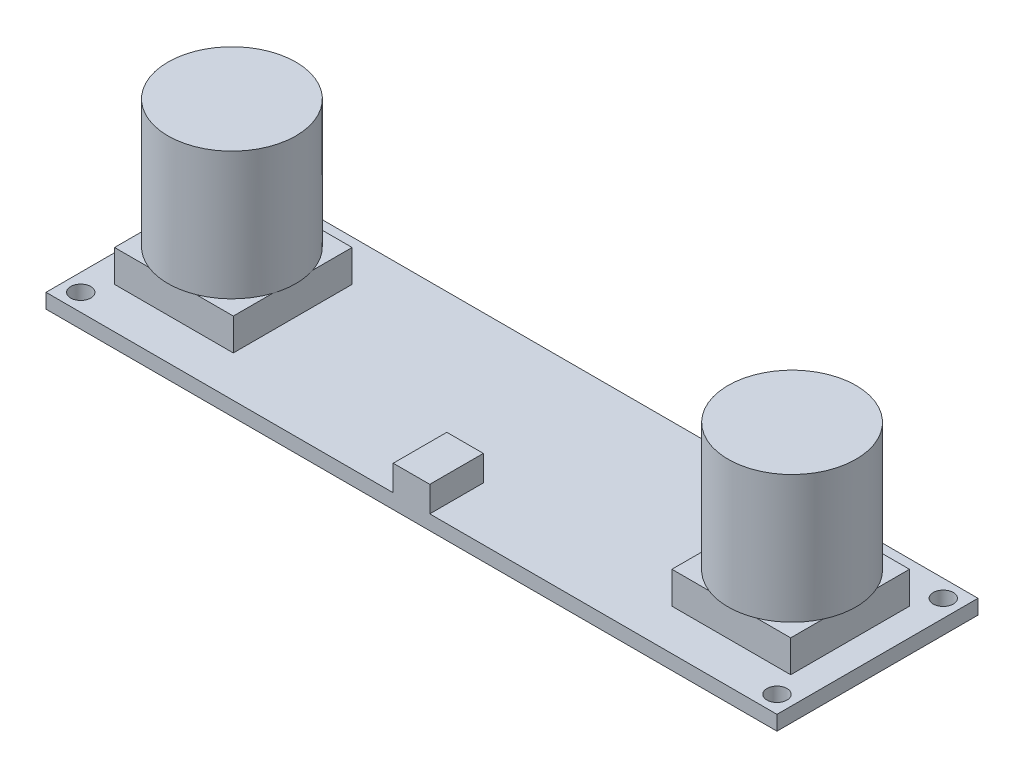
SolidWorks part; units mm, degrees
ref_plane "前视基准面" through (0, 0, 0) normal (0, 0, 1) x (1, 0, 0)
ref_plane "上视基准面" through (0, 0, 0) normal (0, 1, 0) x (1, 0, 0)
ref_plane "右视基准面" through (0, 0, 0) normal (1, 0, 0) x (0, 0, -1)
other "Configuration Table"
sketch "草图1" plane through (0, 0, 0) normal (0, 1, 0) x (1, 0, 0)
  line L1 (40, -11) -> (-40, -11)
  line L2 (40, -11) -> (40, 11)
  line L3 (40, 11) -> (-40, 11)
  line L4 (-40, -11) -> (-40, 11)
  line L5 (40, -11) -> (-40, 11) construction
  line L6 (40, 11) -> (-40, -11) construction
  point P0 (0, 0)
  dimension "D1" = 80
  dimension "D2" = 22
extrude "凸台-拉伸1" add sketch "草图1" along normal blind 1.6
sketch "草图2" plane through (0, 1.6, 0) normal (0, 1, 0) x (1, 0, 0)
  line L0 (-40, 0) -> (40, 0) construction
  line L1 (-40, 11) -> (-40, -11) construction
  line L2 (40, -11) -> (40, 11) construction
  line L3 (0, 11) -> (0, -11) construction
  line L4 (40, 11) -> (-40, 11) construction
  line L5 (-40, -11) -> (40, -11) construction
  line L6 (37, -6.5) -> (37, 6.5)
  line L7 (-24, -6.5) -> (-37, -6.5)
  line L8 (-24, -6.5) -> (-24, 6.5)
  line L9 (-24, 6.5) -> (-37, 6.5)
  line L10 (-37, -6.5) -> (-37, 6.5)
  line L11 (-24, -6.5) -> (-37, 6.5) construction
  line L12 (-24, 6.5) -> (-37, -6.5) construction
  line L13 (24, -6.5) -> (37, -6.5)
  line L14 (24, -6.5) -> (24, 6.5)
  line L15 (24, 6.5) -> (37, 6.5)
  point P12 (-30.5, 0)
  dimension "D1" = 3
  dimension "D2" = 13
extrude "凸台-拉伸2" add sketch "草图2" along normal blind 3.5
ref_plane "基准面1" through (0, 5.1, 0) normal (0, 1, 0) x (1, 0, 0)
sketch "草图4" plane through (0, 5.1, 0) normal (0, 1, 0) x (1, 0, 0)
  line L0 (-38.1, 0) -> (-23.2, 0) construction
  line L5 (0, 11) -> (0, -11) construction
  line L6 (40, 11) -> (-40, 11) construction
  line L7 (-40, -11) -> (40, -11) construction
  circle A0 centre (-30.65, 0) radius 7
  circle A1 centre (30.65, 0) radius 7
extrude "凸台-拉伸3" add sketch "草图4" along normal blind 14
sketch "草图5" plane through (0, 1.6, 0) normal (0, 1, 0) x (1, 0, 0)
  line L0 (0, 11) -> (0, -11) construction
  line L1 (40, 11) -> (-40, 11) construction
  line L2 (-40, -11) -> (40, -11) construction
  line L3 (-40, 0) -> (0, 0) construction
  line L4 (-40, 11) -> (-40, -11) construction
  line L5 (0, 0) -> (40, 0) construction
  line L6 (40, -11) -> (40, 11) construction
  circle A0 centre (-38.1, 9.1) radius 1.1
  circle A1 centre (-38.1, -9.1) radius 1.1
  circle A2 centre (38.1, -9.1) radius 1.1
  circle A3 centre (38.1, 9.1) radius 1.1
  dimension "D1" = 9.1
  dimension "D2" = 38.1
extrude "切除-拉伸1" cut sketch "草图5" against normal through all
sketch "草图6" plane through (0, 1.6, 0) normal (0, 1, 0) x (1, 0, 0)
  line L0 (-40, -11) -> (40, -11) construction
  line L1 (0, -11) -> (2, -11) construction
  line L2 (0, -11) -> (-2, -11)
  line L3 (-2, -11) -> (-2, -5.1363)
  line L4 (-2, -5.1363) -> (2, -5.1363)
  line L5 (2, -5.1363) -> (2, -11)
  line L6 (0, -11) -> (2, -11)
extrude "凸台-拉伸4" add sketch "草图6" along normal blind 2.8
